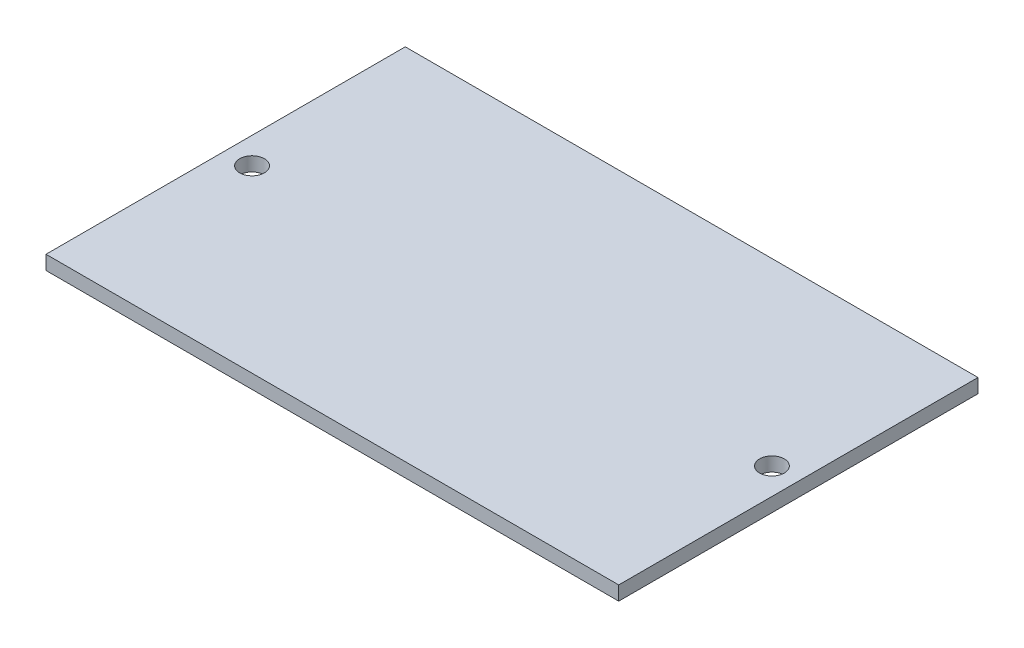
SolidWorks part; units mm, degrees
ref_plane "Front Plane" through (0, 0, 0) normal (0, 0, 1) x (1, 0, 0)
ref_plane "Top Plane" through (0, 0, 0) normal (0, 1, 0) x (1, 0, 0)
ref_plane "Right Plane" through (0, 0, 0) normal (1, 0, 0) x (0, 0, -1)
sketch "Sketch1" plane through (0, 0, 0) normal (0, 1, 0) x (1, 0, 0)
  line L1 (40.65, -25.5) -> (-40.65, -25.5)
  line L2 (40.65, -25.5) -> (40.65, 25.5)
  line L3 (40.65, 25.5) -> (-40.65, 25.5)
  line L4 (-40.65, -25.5) -> (-40.65, 25.5)
  line L5 (40.65, -25.5) -> (-40.65, 25.5) construction
  line L6 (40.65, 25.5) -> (-40.65, -25.5) construction
  point P0 (0, 0)
  dimension "D1" = 51
  dimension "D2" = 81.3
extrude "Boss-Extrude1" add sketch "Sketch1" along normal blind 2
sketch "Sketch2" plane through (0, 2, 0) normal (0, 1, 0) x (1, 0, 0)
  line L0 (40.65, 0) -> (-40.65, 0) construction
  line L1 (-40.65, 25.5) -> (-40.65, -25.5) construction
  line L2 (0, -25.5) -> (0, 25.5) construction
  line L3 (40.65, 25.5) -> (-40.65, 25.5) construction
  circle A0 centre (-36.9, 0) radius 1.75
  circle A2 centre (36.9, 0) radius 1.75
  point P6 (0, 0)
  point P14 (0, 0)
  dimension "D1" = 3.5
  dimension "D2" = 3.75
extrude "Cut-Extrude1" cut sketch "Sketch2" against normal up to surface (2 mm away) up to face at (0, 0, 0)
